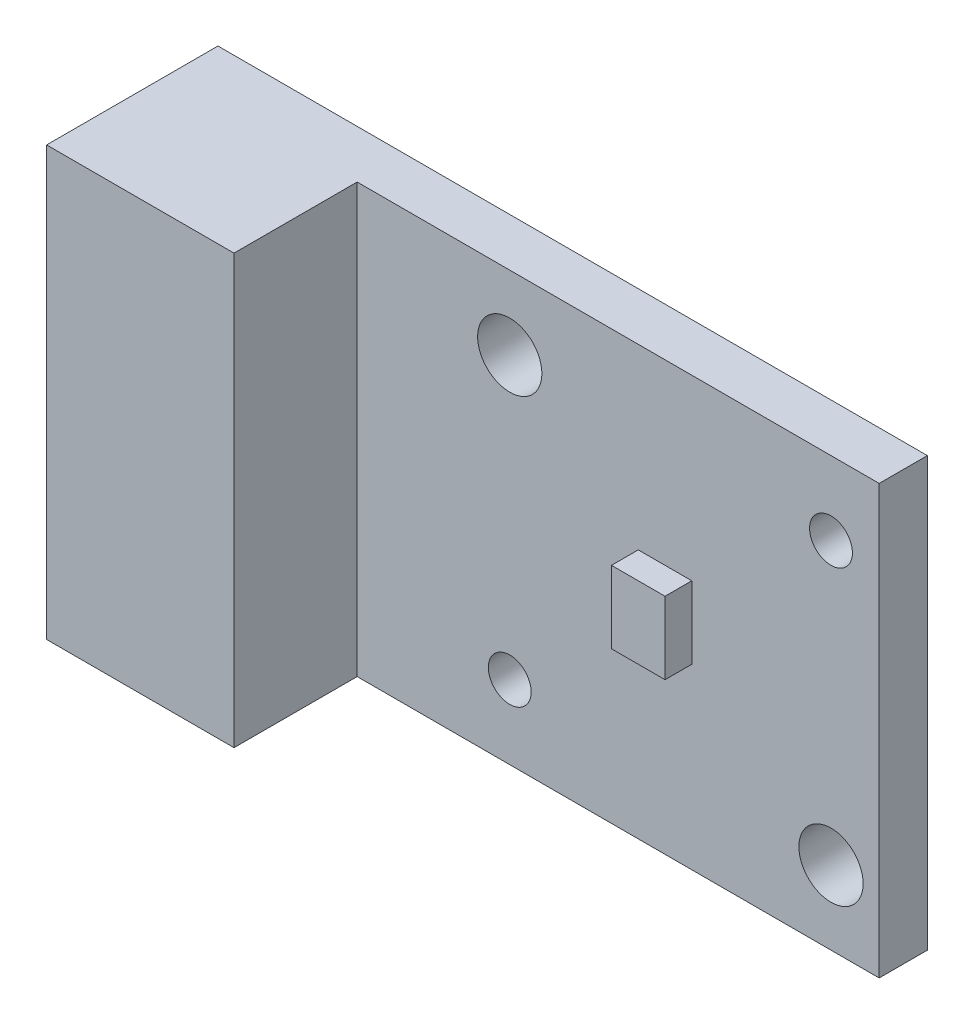
SolidWorks part; units mm, degrees
material "PCB"
ref_plane "Front Plane" through (0, 0, 0) normal (0, 0, 1) x (1, 0, 0)
ref_plane "Top Plane" through (0, 0, 0) normal (0, 1, 0) x (1, 0, 0)
ref_plane "Right Plane" through (0, 0, 0) normal (1, 0, 0) x (0, 0, -1)
sketch "Sketch2" plane through (0, 0, 0) normal (0, 0, 1) x (1, 0, 0)
  line L1 (0, 0) -> (26.5, 0)
  line L2 (0, 0) -> (0, 16)
  line L3 (0, 16) -> (26.5, 16)
  line L4 (26.5, 0) -> (26.5, 16)
  dimension "D1" = 26.5
  dimension "D2" = 16
extrude "Boss-Extrude1" add sketch "Sketch2" along normal blind 1.8
sketch "Sketch3" plane through (0, 0, 1.8) normal (0, 0, 1) x (1, 0, 0)
  line L0 (26.5, 16) -> (0, 16) construction
  line L1 (0, 0) -> (7, 0)
  line L2 (0, 0) -> (0, 16)
  line L3 (0, 16) -> (7, 16)
  line L4 (7, 0) -> (7, 16)
  dimension "D1" = 7
extrude "Boss-Extrude2" add sketch "Sketch3" along normal blind 4.6
sketch "Sketch4" plane through (0, 0, 1.8) normal (0, 0, 1) x (1, 0, 0)
  line L0 (26.5, 16) -> (7, 16) construction
  line L1 (17.5, 6.65) -> (19.5, 6.65)
  line L2 (17.5, 6.65) -> (17.5, 9.35)
  line L3 (17.5, 9.35) -> (19.5, 9.35)
  line L4 (19.5, 6.65) -> (19.5, 9.35)
  line L5 (17.5, 6.65) -> (19.5, 9.35) construction
  line L6 (17.5, 9.35) -> (19.5, 6.65) construction
  line L7 (26.5, 0) -> (26.5, 16) construction
  point P0 (18.5, 8)
  dimension "D1" = 8
  dimension "D2" = 2
  dimension "D3" = 2.7
  dimension "D4" = 8
extrude "Boss-Extrude3" add sketch "Sketch4" along normal blind 1
sketch "Sketch5" plane through (0, 0, 1.8) normal (0, 0, 1) x (1, 0, 0)
  line L0 (0, 0) -> (26.5, 0) construction
  line L2 (26.5, 0) -> (26.5, 16) construction
  circle A0 centre (24.7, 13.25) radius 0.8
  circle A1 centre (12.7, 2.75) radius 0.8
  circle A2 centre (24.7, 2.75) radius 1.2
  circle A3 centre (12.7, 13.25) radius 1.2
  dimension "D4" = 1.6
  dimension "D5" = 2.4
  dimension "D6" = 13.8
  dimension "D1" = 12
  dimension "D2" = 10.5
  dimension "D3" = 2.75
extrude "Cut-Extrude1" cut sketch "Sketch5" against normal through all
